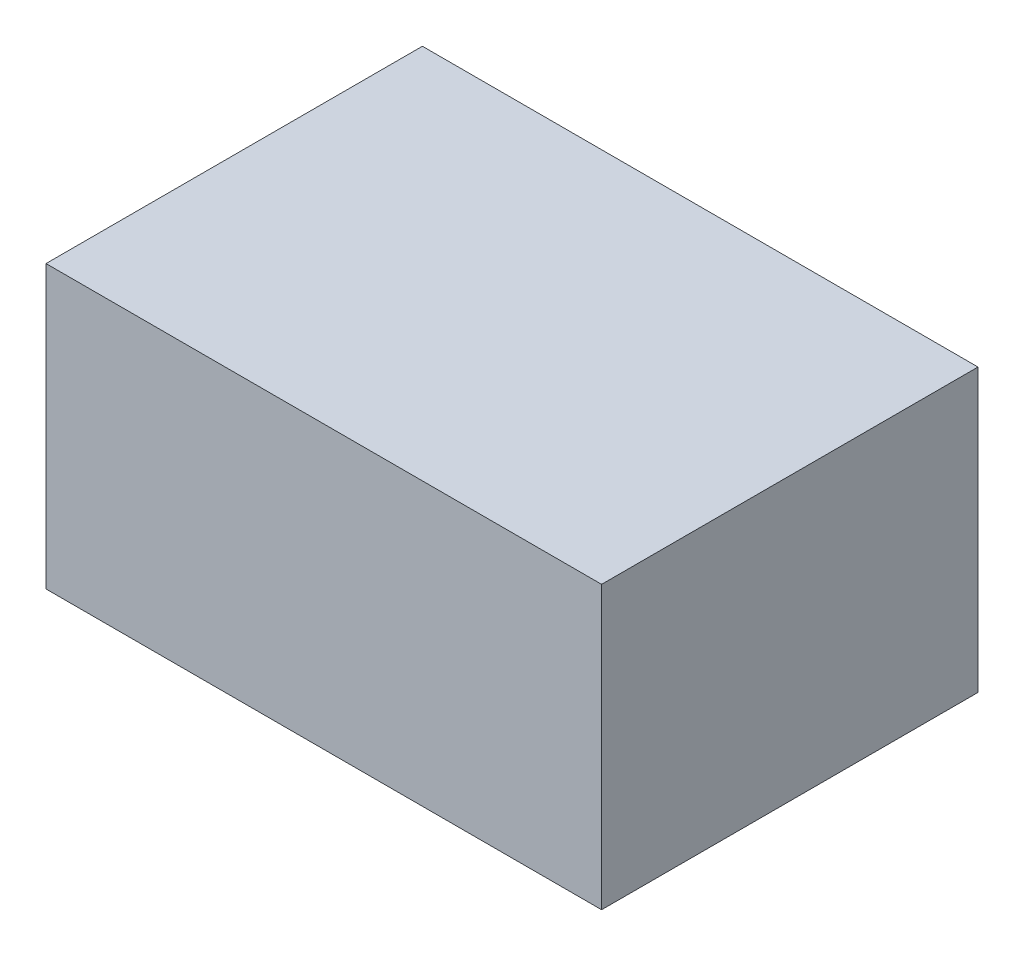
SolidWorks part; units mm, degrees
ref_plane "Ebene vorne" through (0, 0, 0) normal (0, 0, 1) x (1, 0, 0)
ref_plane "Ebene oben" through (0, 0, 0) normal (0, 1, 0) x (1, 0, 0)
ref_plane "Ebene rechts" through (0, 0, 0) normal (1, 0, 0) x (0, 0, -1)
sketch "Skizze1" plane through (0, 0, 0) normal (0, 1, 0) x (1, 0, 0)
  line L0 (0, 29.1723) -> (0, 28.1876) construction
  line L1 (0, 28.1876) -> (0, -23.264) construction
  line L2 (-44.0276, 0) -> (39.4275, 0) construction
  line L4 (-39.4275, 26.7105) -> (39.4275, 26.7105)
  line L5 (-39.4275, 26.7105) -> (-39.4275, -26.7105)
  line L6 (-39.4275, -26.7105) -> (39.4275, -26.7105)
  line L7 (39.4275, 26.7105) -> (39.4275, -26.7105)
  line L8 (-39.4275, 26.7105) -> (39.4275, -26.7105) construction
  line L9 (-39.4275, -26.7105) -> (39.4275, 26.7105) construction
  point P6 (0, 0)
extrude "Aufsatz-Linear austragen2" add sketch "Skizze1" along normal mid plane 40
